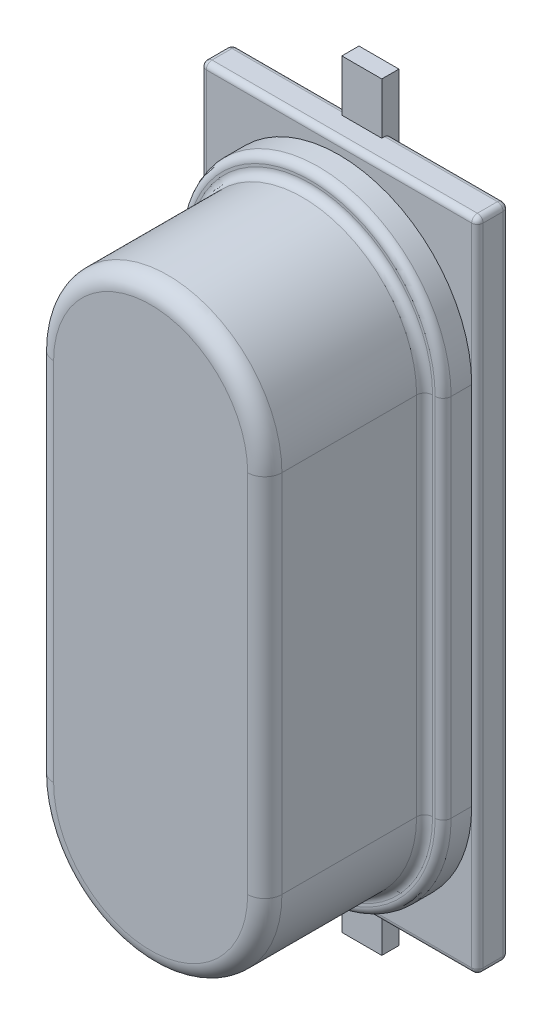
SolidWorks part; units mm, degrees
ref_plane "Plane1" through (0, 0, 0) normal (0, 0, 1) x (1, 0, 0)
ref_plane "Plane2" through (0, 0, 0) normal (0, 1, 0) x (1, 0, 0)
ref_plane "Plane3" through (0, 0, 0) normal (1, 0, 0) x (0, 0, -1)
sketch "Sketch2" plane through (0, 0, 0) normal (0, 0, 1) x (1, 0, 0)
  line L0 (0, 5.525) -> (0, 3.2) construction
  line L1 (0, 0) -> (2.35, 0) construction
  line L2 (2.325, 3.2) -> (2.325, -3.2)
  line L3 (-2.325, 3.2) -> (-2.325, -3.2)
  line L4 (0, -5.525) -> (4.5178, -5.525) construction
  line L5 (0, 5.525) -> (4.226, 5.525) construction
  arc A0 (2.325, 3.2) -> (-2.325, 3.2) centre (0, 3.2) ccw
  arc A1 (2.325, -3.2) -> (-2.325, -3.2) centre (0, -3.2) cw
  dimension "D1" = 11.05
  dimension "D2" = 4.65
extrude "Boss-Extrude1" add sketch "Sketch2" along normal blind 0.5 from offset 0.7
sketch "Sketch3" plane through (0, 0, 1.2) normal (0, 0, 1) x (1, 0, 0)
  line L0 (0, 5.2) -> (5.872, 5.2) construction
  line L1 (0, -5.2) -> (5.5747, -5.2) construction
  line L2 (-2, -3.2) -> (-2, 3.2)
  line L3 (2, -3.2) -> (2, 3.2)
  line L4 (0, 5.2) -> (0, 7.8524) construction
  line L5 (0, -5.2) -> (0, -1.7444) construction
  line L6 (0, 0) -> (3.9198, 0) construction
  arc A2 (2, 3.2) -> (-2, 3.2) centre (0, 3.2) ccw
  arc A3 (-2, -3.2) -> (2, -3.2) centre (0, -3.2) ccw
  dimension "D1" = 4
  dimension "D2" = 10.4
extrude "Boss-Extrude2" add sketch "Sketch3" along normal blind 2.8
fillet "Fillet2" radius 0.14 8 edges at (0, 5.525, 1.2) (0, 5.2, 1.2) (-2.325, 0, 1.2) (2.325, 0, 1.2) (-2, 0, 1.2) (2, 0, 1.2) (0, -5.525, 1.2) (0, -5.2, 1.2)
fillet "Скругление3" radius 0.3 4 edges at (-2, 0, 4) (0, 5.2, 4) (2, 0, 4) (0, -5.2, 4)
sketch "Эскиз3" plane through (0, 0, 0.7) normal (0, 0, 1) x (1, 0, 0)
  line L1 (2.425, -5.75) -> (-2.425, -5.75)
  line L2 (2.425, -5.75) -> (2.425, 5.75)
  line L3 (2.425, 5.75) -> (-2.425, 5.75)
  line L4 (-2.425, -5.75) -> (-2.425, 5.75)
  line L5 (2.425, -5.75) -> (-2.425, 5.75) construction
  line L6 (2.425, 5.75) -> (-2.425, -5.75) construction
  point P0 (0, 0)
  dimension "D1" = 11.5
  dimension "D2" = 4.85
extrude "Бобышка-Вытянуть3" add sketch "Эскиз3" against normal blind 0.55 separate body
fillet "Скругление4" radius 0.1 12 edges at (0, -5.75, 0.15) (2.425, 0, 0.15) (0, 5.75, 0.15) (-2.425, 0, 0.15) (2.425, 5.75, 0.425) (0, 5.75, 0.7) (-2.425, 5.75, 0.425) (-2.425, 0, 0.7) (-2.425, -5.75, 0.425) (2.425, 0, 0.7) (0, -5.75, 0.7) (2.425, -5.75, 0.425)
sketch "Эскиз1" plane through (0, 0, 0) normal (0, 0, -1) x (-1, 0, 0)
  line L0 (0, 0) -> (0, 8.1352) construction
  line L1 (0, 0) -> (3.931, 0) construction
  line L2 (-0.35, -2.44) -> (-0.35, -6.65)
  line L3 (0.35, 2.44) -> (-0.35, 2.44)
  line L4 (0.35, 2.44) -> (0.35, 6.65)
  line L5 (0.35, 6.65) -> (-0.35, 6.65)
  line L6 (-0.35, 2.44) -> (-0.35, 6.65)
  line L7 (0.35, 2.44) -> (-0.35, 6.65) construction
  line L8 (0.35, 6.65) -> (-0.35, 2.44) construction
  line L9 (0.35, -2.44) -> (-0.35, -2.44)
  line L10 (0.35, -2.44) -> (0.35, -6.65)
  line L11 (0.35, -6.65) -> (-0.35, -6.65)
  point P3 (0, 4.545)
  dimension "D1" = 0.7
  dimension "D2" = 13.3
  dimension "D3" = 4.88
extrude "Бобышка-Вытянуть4" add sketch "Эскиз1" against normal blind 0.3 separate body
